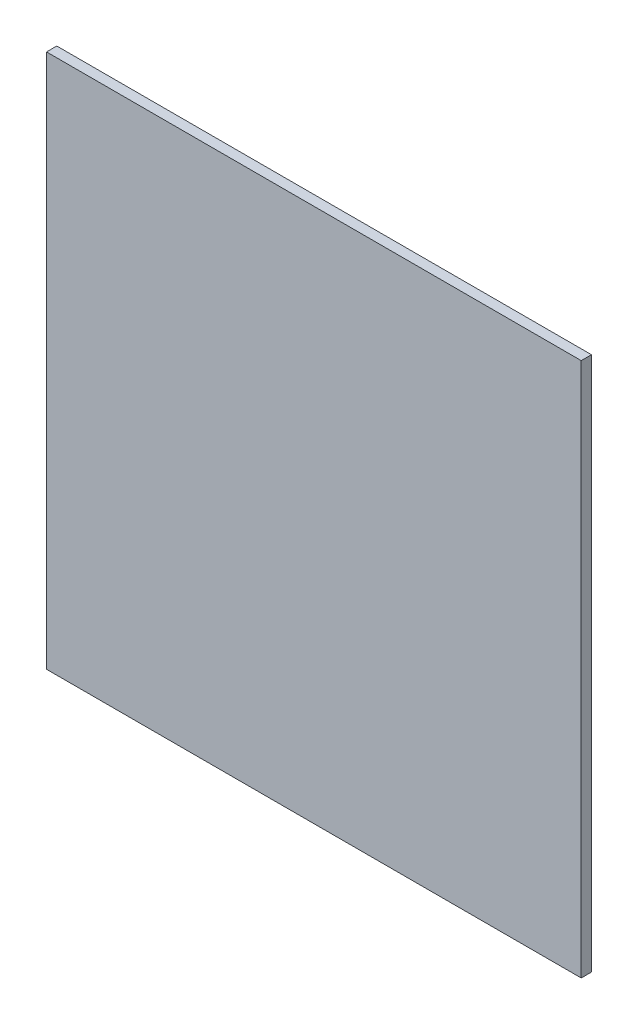
SolidWorks part; units mm, degrees
ref_plane "Płaszczyzna przednia" through (0, 0, 0) normal (0, 0, 1) x (1, 0, 0)
ref_plane "Płaszczyzna górna" through (0, 0, 0) normal (0, 1, 0) x (1, 0, 0)
ref_plane "Płaszczyzna prawa" through (0, 0, 0) normal (1, 0, 0) x (0, 0, -1)
sketch "Szkic1" plane through (0, 0, 0) normal (0, 0, 1) x (1, 0, 0)
  line L1 (0, 0) -> (470, 0)
  line L2 (0, 0) -> (0, 470)
  line L3 (0, 470) -> (470, 470)
  line L4 (470, 0) -> (470, 470)
  dimension "D1" = 470
  dimension "D2" = 470
extrude "Dodanie-wyciągnięcie1" add sketch "Szkic1" against normal blind 9
